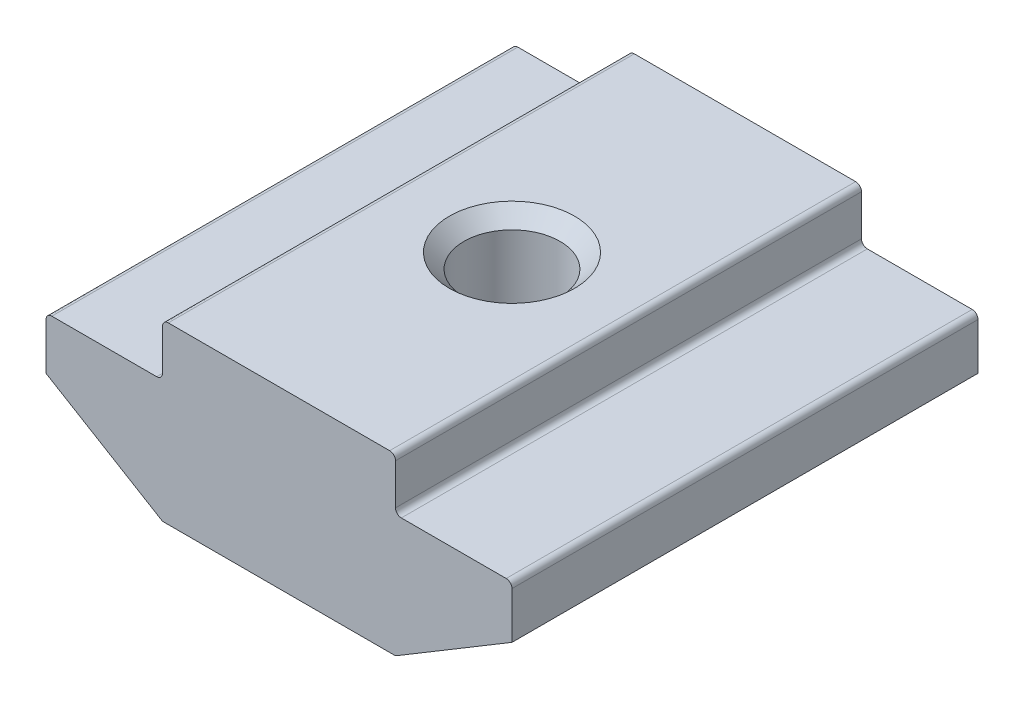
SolidWorks part; units mm, degrees
ref_plane "Спереди" through (0, 0, 0) normal (0, 0, 1) x (1, 0, 0)
ref_plane "Сверху" through (0, 0, 0) normal (0, 1, 0) x (1, 0, 0)
ref_plane "Справа" through (0, 0, 0) normal (1, 0, 0) x (0, 0, -1)
sketch "Эскиз1" plane through (0, 0, 0) normal (0, 0, 1) x (1, 0, 0)
  line L0 (4, 0) -> (-4, 0)
  line L1 (-4, 0) -> (-4, -1.8)
  line L2 (-4, -1.8) -> (-8, -1.8)
  line L3 (-8, -1.8) -> (-8, -3.6)
  line L4 (-8, -3.6) -> (-4, -6)
  line L5 (-4, -6) -> (4, -6)
  line L6 (0, -6) -> (0, 0) construction
  line L7 (8, -3.6) -> (4, -6)
  line L8 (8, -1.8) -> (8, -3.6)
  line L9 (4, -1.8) -> (8, -1.8)
  line L10 (4, 0) -> (4, -1.8)
  point P3 (-4, -0.9)
  point P9 (-2.7421, -5)
  point P10 (-5, -1.6182)
  dimension "D1" = 8
  dimension "D2" = 16
  dimension "D4" = 6
  dimension "D5" = 4.2
extrude "Бобышка-Вытянуть1" add sketch "Эскиз1" along normal mid plane 16
hole_wizard "Отверстие обработанное метчиком M42" positions "Эскиз2" profile "Эскиз4" tap size "M4" standard "ISO" end condition through all
sketch "Эскиз2" plane through (0, 0, 0) normal (0, 1, 0) x (1, 0, 0)
  point P0 (0, 0)
sketch "Эскиз4" plane through (0, 0, 0) normal (1, 0, 0) x (0, 0, 1)
  line L0 (0, 0) -> (0, 6)
  line L1 (0, 6) -> (2.15, 6)
  line L2 (1.65, 5.5) -> (1.65, 0.5)
  line L3 (1.65, 0.5) -> (2.15, 0)
  line L5 (2.15, 0) -> (0, 0)
  line L6 (-1.65, 0.5) -> (-2.15, 0) construction
  line L7 (2.15, 6) -> (1.65, 5.5)
  line L8 (-2.15, 6) -> (-1.65, 5.5) construction
  line L11 (0, -6.35) -> (0, 107.95) construction
  dimension "Диаметр проходного сверла" = 3.3
  dimension "Глубина проходного сверла" = 6
  dimension "Диаметр передней зенковки" = 4.3
  dimension "Угол передней зенковки" = 90
  dimension "Диаметр задней зенковки" = 4.3
  dimension "Угол задней зенковки" = 90
cosmetic thread "Отверстие резьбы1" parameters "D2"=4
fillet "Скругление1" radius 0.2 8 edges at (4, -6, 0) (-4, -6, 0) (8, -1.8, 0) (4, -1.8, 0) (4, 0, 0) (-4, 0, 0) (-8, -1.8, 0) (-4, -1.8, 0)
